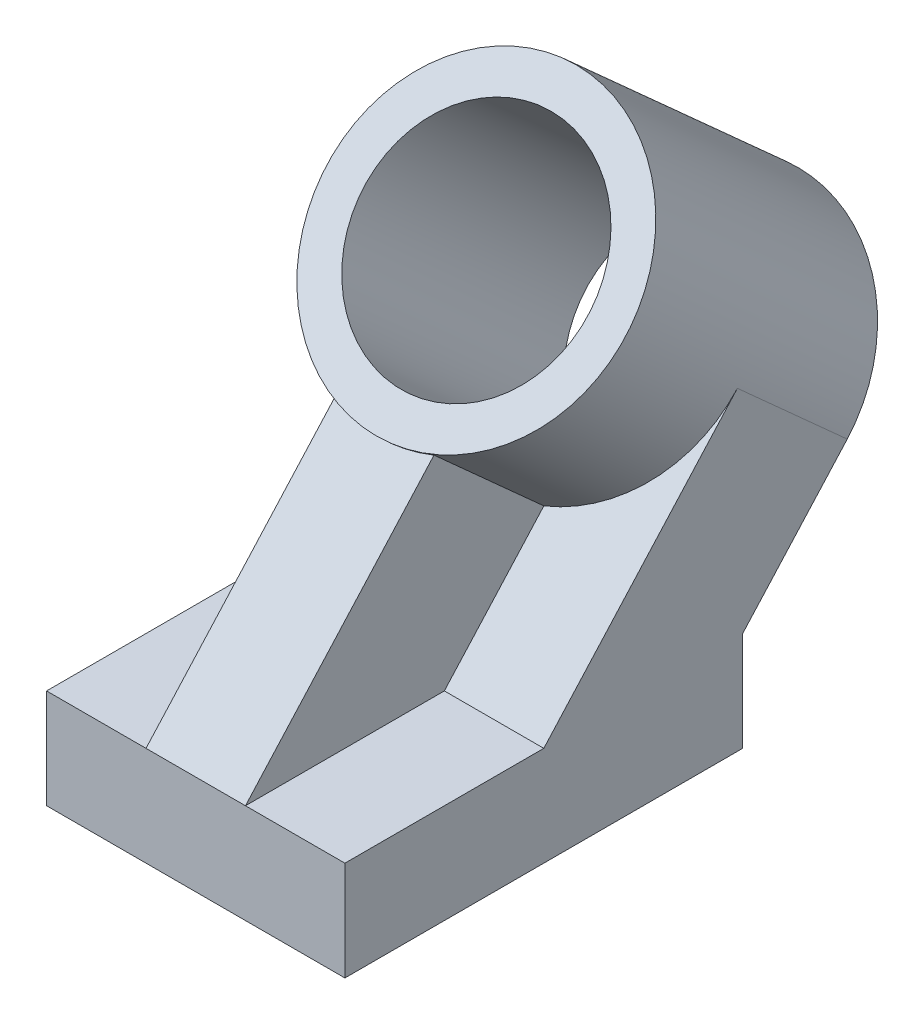
SolidWorks part; units mm, degrees
material "6061 Alloy"
ref_plane "Front Plane" through (0, 0, 0) normal (0, 0, 1) x (1, 0, 0)
ref_plane "Top Plane" through (0, 0, 0) normal (0, 1, 0) x (1, 0, 0)
ref_plane "Right Plane" through (0, 0, 0) normal (1, 0, 0) x (0, 0, -1)
sketch "Sketch1" plane through (0, 0, 0) normal (1, 0, 0) x (0, 0, -1)
  line L0 (0, 0) -> (0, 25.4)
  line L1 (0, 25.4) -> (50.8, 25.4)
  line L2 (50.8, 25.4) -> (100.2446, 80.3137)
  line L3 (100.2446, 80.3137) -> (128.2996, 55.0529)
  line L5 (101.6, 0) -> (0, 0)
  line L6 (101.6, 0) -> (101.6, 25.4)
  line L7 (101.6, 25.4) -> (128.2996, 55.0529)
  line L8 (101.6, 25.4) -> (164.0114, 25.4) construction
  dimension "D1" = 25.4
  dimension "D2" = 101.6
  dimension "D3" = 50.8
  dimension "D4" = 114.3
  dimension "D5" = 48
  dimension "D6" = 25.4
extrude "Boss-Extrude1" add sketch "Sketch1" along normal mid plane 76.2
ref_plane "Circle plane" through (0, -13.8884, -15.4246) normal (0, 0.6691, 0.7431) x (1, 0, 0)
ref_plane "Plane2" through (0, 11.3725, 12.6304) normal (0, 0.6691, 0.7431) x (1, 0, 0)
sketch "Sketch3" plane through (0, 11.3725, 12.6304) normal (0, 0.6691, 0.7431) x (1, 0, 0)
  line L0 (38.1, 18.8759) -> (-38.1, 18.8759) construction
  line L1 (-12.7, 18.8759) -> (12.7, 18.8759)
  line L2 (-12.7, 18.8759) -> (-12.7, 107.037)
  line L3 (-12.7, 107.037) -> (12.7, 107.037)
  line L4 (12.7, 18.8759) -> (12.7, 107.037)
  point P6 (0, 18.8759)
  dimension "D1" = 25.4
extrude "Boss-Extrude2" add sketch "Sketch3" against normal up to next contours L2 L1 L4 L3
ref_plane "Plane3" through (0, -39.1492, -43.4796) normal (0, -0.6691, -0.7431) x (-1, 0, 0)
sketch "Sketch4" plane through (0, -39.1492, -43.4796) normal (0, -0.6691, -0.7431) x (-1, 0, 0)
  line L0 (-38.1, 126.7614) -> (38.1, 126.7614) construction
  circle A0 centre (0, 126.7614) radius 38.1
extrude "Boss-Extrude3" add sketch "Sketch4" against normal blind 76.2
sketch "Sketch5" plane through (0, -39.1492, -43.4796) normal (0, -0.6691, -0.7431) x (-1, 0, 0)
  circle A0 centre (0, 126.7614) radius 28.575
  dimension "D1" = 57.15
extrude "Cut-Extrude1" cut sketch "Sketch5" against normal blind 76.2
